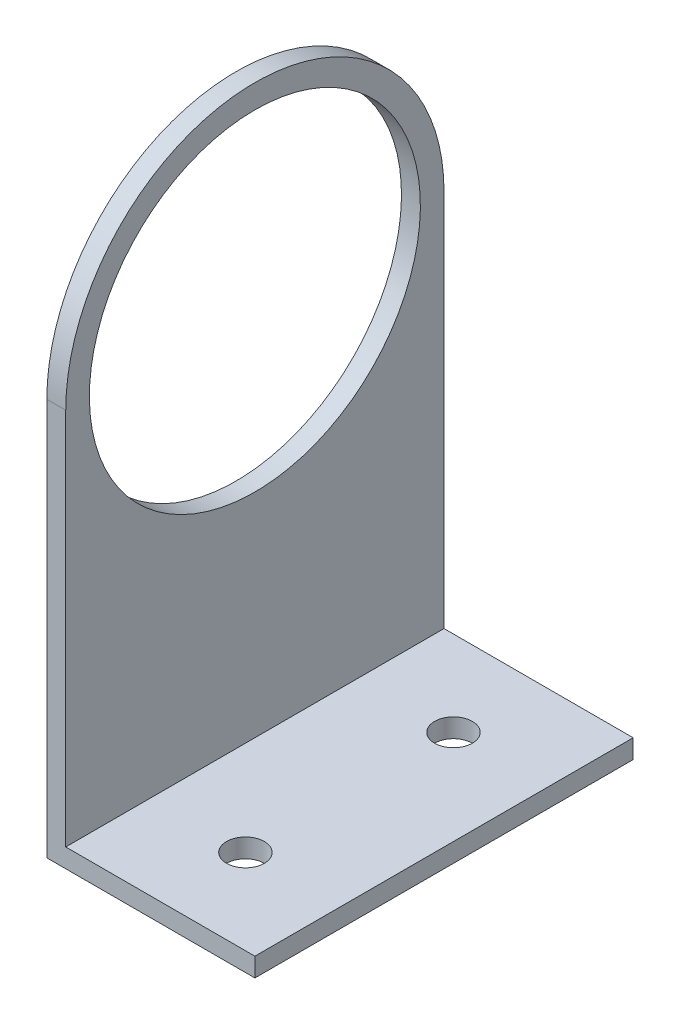
SolidWorks part; units mm, degrees
material "7075-T6 (SN)"
ref_plane "Front Plane" through (0, 0, 0) normal (0, 0, 1) x (1, 0, 0)
ref_plane "Top Plane" through (0, 0, 0) normal (0, 1, 0) x (1, 0, 0)
ref_plane "Right Plane" through (0, 0, 0) normal (1, 0, 0) x (0, 0, -1)
sketch "Sketch1" plane through (0, 0, 0) normal (0, 0, 1) x (1, 0, 0)
  line L0 (0, 0) -> (0, 62)
  line L1 (0, 62) -> (2, 62)
  line L2 (2, 62) -> (2, 2)
  line L3 (2, 2) -> (22, 2)
  line L4 (22, 2) -> (22, 0)
  line L5 (22, 0) -> (0, 0)
  dimension "D1" = 2
  dimension "D2" = 2
  dimension "D3" = 20
  dimension "D4" = 60
extrude "Boss-Extrude1" add sketch "Sketch1" along normal blind 40
sketch "Sketch2" plane through (2, 0, 0) normal (1, 0, 0) x (0, 0, -1)
  line L0 (-44.3425, 42) -> (6.0553, 42) construction
  line L1 (-20, 65.365) -> (-20, 20.4295) construction
  line L2 (-40, 62) -> (0, 62) construction
  circle A0 centre (-20, 42) radius 17.5
  point P6 (-20, 62)
  dimension "D2" = 35
  dimension "D1" = 20
extrude "Cut-Extrude1" cut sketch "Sketch2" against normal up to next
sketch "Sketch5" plane through (2, 0, 0) normal (1, 0, 0) x (0, 0, -1)
  line L0 (-40, 42) -> (-40, 62)
  line L1 (-40, 62) -> (0, 62)
  line L2 (0, 62) -> (0, 42)
  arc A0 (0, 42) -> (-40, 42) centre (-20, 42) ccw
  line M3 (0, 2) -> (0, 62)
  line M4 (0, 62) -> (-40, 62)
  line M5 (-40, 62) -> (-40, 2)
extrude "Cut-Extrude2" cut sketch "Sketch5" against normal up to next contours A0 L1 M5 | A0 M3 M4
sketch "Sketch6" plane through (0, 2, 0) normal (0, 1, 0) x (1, 0, 0)
  line L0 (12, 3.9224) -> (12, -46.9469) construction
  line L1 (28.7999, -20) -> (-7.9342, -20) construction
  line L2 (-7.9342, -31) -> (28.7999, -31) construction
  line L3 (-7.9342, -9) -> (28.7999, -9) construction
  line L4 (22, 0) -> (2, 0) construction
  line L5 (22, -40) -> (22, 0) construction
  circle A0 centre (12, -9) radius 2
  circle A1 centre (12, -31) radius 2
  point P10 (12, 0)
  point P13 (22, -20)
  dimension "D3" = 4
  dimension "D4" = 4
  dimension "D1" = 11
  dimension "D2" = 11
extrude "Cut-Extrude3" cut sketch "Sketch6" against normal up to next
